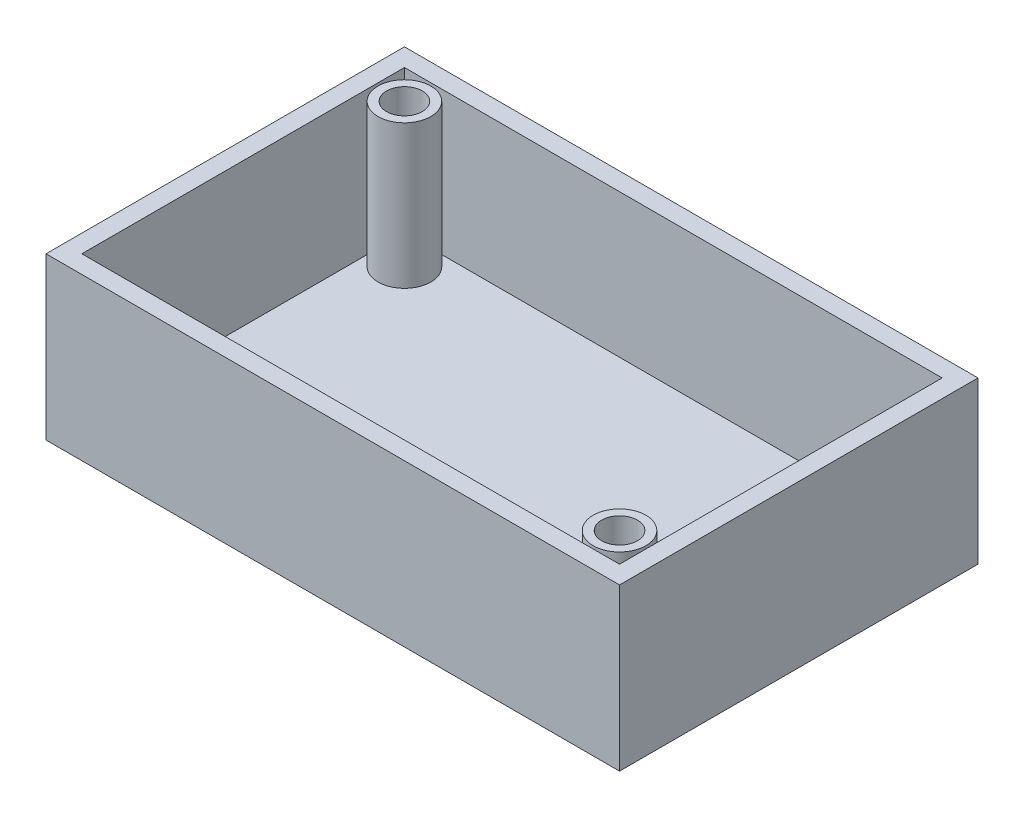
SolidWorks part; units mm, degrees
ref_plane "Front" through (0, 0, 0) normal (0, 0, 1) x (1, 0, 0)
ref_plane "Top" through (0, 0, 0) normal (0, 1, 0) x (1, 0, 0)
ref_plane "Right" through (0, 0, 0) normal (1, 0, 0) x (0, 0, -1)
sketch "Sketch1" plane through (0, 0, 0) normal (0, 1, 0) x (1, 0, 0)
  line L1 (-39.0769, 55.5451) -> (62.5231, 55.5451)
  line L2 (-39.0769, 55.5451) -> (-39.0769, -7.9549)
  line L3 (-39.0769, -7.9549) -> (62.5231, -7.9549)
  line L4 (62.5231, 55.5451) -> (62.5231, -7.9549)
  dimension "D1" = 63.5
  dimension "D2" = 101.6
extrude "Boss-Extrude1" add sketch "Sketch1" along normal blind 3.175
sketch "Sketch2" plane through (0, 3.175, 0) normal (0, 1, 0) x (1, 0, 0)
  line L12 (-35.9019, -4.7799) -> (59.3481, -4.7799)
  line L13 (-35.9019, 52.3701) -> (-35.9019, -4.7799)
  line L14 (59.3481, 52.3701) -> (-35.9019, 52.3701)
  line L15 (59.3481, -4.7799) -> (59.3481, 52.3701)
  line L16 (-35.9019, -4.7799) -> (59.3481, -4.7799)
  line L17 (-35.9019, 52.3701) -> (-35.9019, -4.7799)
  line L18 (59.3481, 52.3701) -> (-35.9019, 52.3701)
  line L19 (59.3481, -4.7799) -> (59.3481, 52.3701)
  line L24 (-39.0769, 55.5451) -> (-39.0769, -7.9549)
  line L25 (-39.0769, -7.9549) -> (62.5231, -7.9549)
  line L26 (62.5231, -7.9549) -> (62.5231, 55.5451)
  line L27 (62.5231, 55.5451) -> (-39.0769, 55.5451)
  line L28 (-39.0769, 55.5451) -> (-39.0769, -7.9549)
  line L29 (-39.0769, -7.9549) -> (62.5231, -7.9549)
  line L30 (62.5231, -7.9549) -> (62.5231, 55.5451)
  line L31 (62.5231, 55.5451) -> (-39.0769, 55.5451)
  dimension "D1" = 3.175
  dimension "D2" = 0
extrude "Boss-Extrude3" add sketch "Sketch2" along normal blind 25.4
sketch "Sketch3" plane through (0, 0, 0) normal (0, -1, 0) x (1, 0, 0)
  circle A0 centre (47.8144, -23.7773) radius 2.1411
extrude "Cut-Extrude1" cut sketch "Sketch3" against normal blind 3.175
ref_plane "Plane1" through (62.5231, 28.575, -55.5451) normal (-1, 0, 0) x (0, 0, 1)
sketch "Sketch5" plane through (0, 3.175, 0) normal (0, 1, 0) x (1, 0, 0)
  line L0 (-35.9019, 52.3701) -> (-35.9019, -4.7799) construction
  line L1 (59.3481, 52.3701) -> (-35.9019, 52.3701) construction
  line L10 (-35.9019, 52.3701) -> (-35.9019, -4.7799)
  line L11 (-35.9019, -4.7799) -> (59.3481, -4.7799)
  line L12 (59.3481, -4.7799) -> (59.3481, 52.3701)
  line L13 (59.3481, 52.3701) -> (-35.9019, 52.3701)
  line L14 (-35.9019, 52.3701) -> (-35.9019, -4.7799)
  line L15 (-35.9019, -4.7799) -> (59.3481, -4.7799)
  line L16 (59.3481, -4.7799) -> (59.3481, 52.3701)
  line L17 (59.3481, 52.3701) -> (-35.9019, 52.3701)
  circle A0 centre (54.1681, 0.4001) radius 3.175
  circle A1 centre (-30.7269, 47.1901) radius 3.175
  circle A2 centre (-30.7269, 47.1901) radius 4.675
  circle A3 centre (54.1681, 0.4001) radius 4.675
  dimension "D2" = 6.35
  dimension "D6" = 6.35
  dimension "D1" = 5.175
  dimension "D3" = 5.18
  dimension "D7" = 5.18
  dimension "D8" = 5.18
  dimension "D4" = 0
  dimension "D5" = 1.5
  dimension "D9" = 1.5
extrude "Boss-Extrude4" add sketch "Sketch5" along normal blind 25.4 contours A2 A1 | A3 A0
